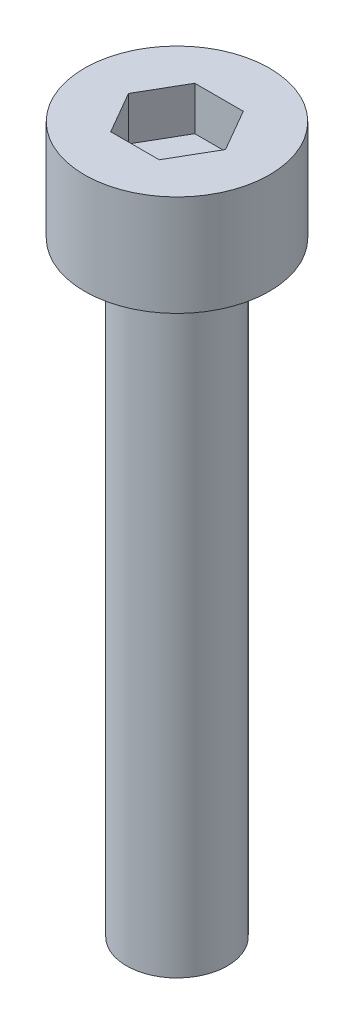
SolidWorks part; units mm, degrees
material "AISI 304"
ref_plane "前视基准面" through (0, 0, 0) normal (0, 0, 1) x (1, 0, 0)
ref_plane "上视基准面" through (0, 0, 0) normal (0, 1, 0) x (1, 0, 0)
ref_plane "右视基准面" through (0, 0, 0) normal (1, 0, 0) x (0, 0, -1)
sketch "草图1" plane through (0, 0, 0) normal (0, 1, 0) x (1, 0, 0)
  circle A0 centre (0, 0) radius 2.75
  dimension "D1" = 5.5
extrude "杯头" add sketch "草图1" along normal blind 3
sketch "草图2" plane through (0, 3, 0) normal (0, 1, 0) x (1, 0, 0)
  line L1 (1.4434, 0) -> (0.7217, 1.25)
  line L2 (0.7217, 1.25) -> (-0.7217, 1.25)
  line L3 (-0.7217, 1.25) -> (-1.4434, 0)
  line L4 (-1.4434, 0) -> (-0.7217, -1.25)
  line L5 (-0.7217, -1.25) -> (0.7217, -1.25)
  line L6 (0.7217, -1.25) -> (1.4434, 0)
  circle A0 centre (0, 0) radius 1.25 construction
  dimension "D1" = 2.5
extrude "内六角口" cut sketch "草图2" against normal blind 1.3
sketch "草图3" plane through (0, 0, 0) normal (0, -1, 0) x (1, 0, 0)
  circle A0 centre (0, 0) radius 1.5
  dimension "D1" = 3
extrude "螺纹长" add sketch "草图3" along normal blind 18
